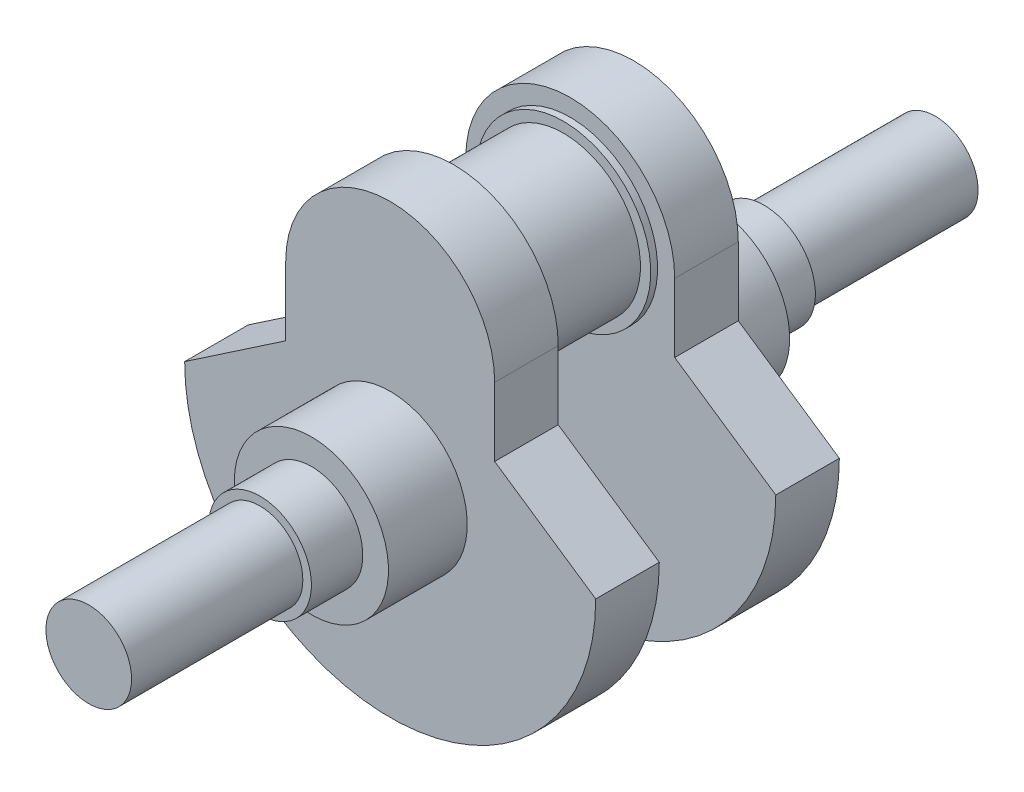
SolidWorks part; units mm, degrees
material "AISI 4340 Steel, normalized"
ref_plane "Front Plane" through (0, 0, 0) normal (0, 0, 1) x (1, 0, 0)
ref_plane "Top Plane" through (0, 0, 0) normal (0, 1, 0) x (1, 0, 0)
ref_plane "Right Plane" through (0, 0, 0) normal (1, 0, 0) x (0, 0, -1)
sketch "Sketch1" plane through (0, 0, 0) normal (0, 0, 1) x (1, 0, 0)
  circle A0 centre (0, 0) radius 12.5
  dimension "D1" = 25
extrude "Boss-Extrude1" add sketch "Sketch1" against normal blind 50
sketch "Sketch3" plane through (0, 0, -50) normal (0, 0, -1) x (-1, 0, 0)
  circle A0 centre (0, 0) radius 15
  dimension "D1" = 30
extrude "Boss-Extrude2" add sketch "Sketch3" along normal blind 15
sketch "Sketch4" plane through (0, 0, -65) normal (0, 0, -1) x (-1, 0, 0)
  circle A0 centre (0, 0) radius 22.5
  dimension "D1" = 45
extrude "Boss-Extrude3" add sketch "Sketch4" along normal blind 23
sketch "Sketch5" plane through (0, 0, -88) normal (0, 0, -1) x (-1, 0, 0)
  line L2 (-30.5, 40) -> (-30.5, 20)
  line L3 (-30.5, 20) -> (-60, -0.0031)
  line L4 (30.5, 40) -> (30.5, 20)
  line L5 (30.5, 20) -> (60, 0)
  arc A0 (-60, 0) -> (60, 0) centre (0, 0) ccw
  arc A1 (30.5, 40) -> (-30.5, 40) centre (0, 40) ccw
  point P3 (0, 40)
  circle M7 centre (0, 0) radius 22.5
  dimension "D1" = 120
  dimension "D3" = 61
  dimension "D2" = 40
  dimension "D4" = 20
  dimension "D5" = 124.14
  dimension "D6" = 124.136
extrude "Boss-Extrude5" add sketch "Sketch5" along normal blind 18.56 contours L4 A1 L2 L3 A0 L5 M7
sketch "Sketch6" plane through (0, 0, -106.56) normal (0, 0, -1) x (-1, 0, 0)
  circle A0 centre (0, 0) radius 22.5
extrude "Boss-Extrude6" add sketch "Sketch6" against normal blind 18.56
sketch "Sketch7" plane through (0, 0, -106.56) normal (0, 0, -1) x (-1, 0, 0)
  circle A1 centre (0, 40) radius 25.5
  point P0 (0, 40)
  dimension "D1" = 40
  dimension "D2" = 51
extrude "Boss-Extrude7" add sketch "Sketch7" along normal blind 2
sketch "Sketch9" plane through (0, 0, -108.56) normal (0, 0, -1) x (-1, 0, 0)
  circle A0 centre (0, 40) radius 22.5
  dimension "D1" = 45
extrude "Boss-Extrude8" add sketch "Sketch9" along normal blind 30
sketch "Sketch11" plane through (0, 0, -138.56) normal (0, 0, -1) x (-1, 0, 0)
  circle A0 centre (0, 40) radius 25.5
  dimension "D1" = 51
extrude "Boss-Extrude9" add sketch "Sketch11" along normal blind 2
sketch "Sketch12" plane through (0, 0, -140.56) normal (0, 0, -1) x (-1, 0, 0)
  line L2 (-30.5, 40) -> (-30.5, 20)
  line L3 (-30.5, 20) -> (-60, 0)
  line L4 (30.5, 40) -> (30.5, 20)
  line L5 (30.5, 20) -> (60, 0)
  arc A0 (-60, 0) -> (60, 0) centre (0, 0) ccw
  arc A1 (30.5, 40) -> (-30.5, 40) centre (0, 40) ccw
extrude "Boss-Extrude10" add sketch "Sketch12" along normal blind 18.56
sketch "Sketch13" plane through (0, 0, -159.12) normal (0, 0, -1) x (-1, 0, 0)
  circle A0 centre (0, 0) radius 22.5
  dimension "D1" = 45
extrude "Boss-Extrude11" add sketch "Sketch13" along normal blind 23
sketch "Sketch14" plane through (0, 0, -182.12) normal (0, 0, -1) x (-1, 0, 0)
  circle A0 centre (0, 0) radius 15
  dimension "D1" = 30
extrude "Boss-Extrude12" add sketch "Sketch14" along normal blind 15
sketch "Sketch15" plane through (0, 0, -197.12) normal (0, 0, -1) x (-1, 0, 0)
  circle A0 centre (0, 0) radius 12.5
  dimension "D1" = 25
extrude "Boss-Extrude13" add sketch "Sketch15" along normal blind 50
